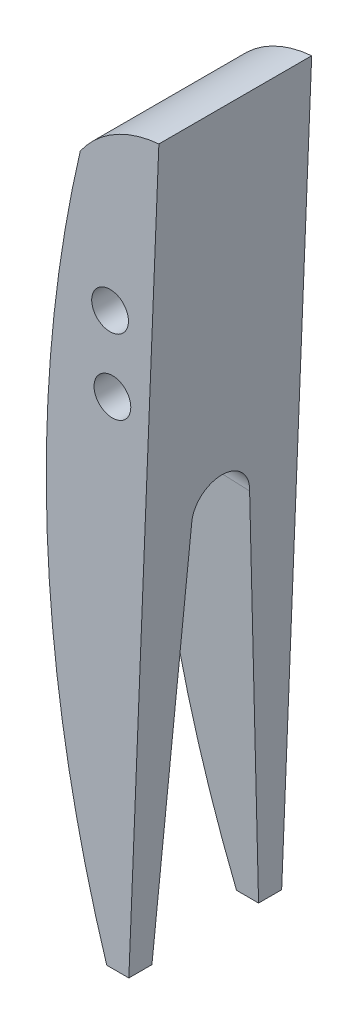
SolidWorks part; units mm, degrees
material "Polyester Resin"
ref_plane "Front Plane" through (0, 0, 0) normal (0, 0, 1) x (1, 0, 0)
ref_plane "Top Plane" through (0, 0, 0) normal (0, 1, 0) x (1, 0, 0)
ref_plane "Right Plane" through (0, 0, 0) normal (1, 0, 0) x (0, 0, -1)
sketch "Sketch1" plane through (0, 0, 0) normal (0, 0, 1) x (1, 0, 0)
  line L0 (23.5472, 52.9813) -> (117.7362, 52.9813) construction
  line L1 (74.1278, 88.7959) -> (72.0004, 36.5744)
  line L2 (672, 1512) -> (3360, 1512) construction
  arc A1 (68.9663, 85.8139) -> (72.0004, 36.5744) centre (153.2214, 66.2924) ccw
  circle A2 centre (70.9254, 77.7224) radius 1.2065
  circle A3 centre (71.0778, 72.8964) radius 1.2065
  arc A5 (74.1278, 88.7959) -> (68.9663, 85.8139) centre (74.7354, 81.7864) ccw
  dimension "D3" = 4.064
  dimension "D4" = 86.487
  dimension "D5" = 2.413
  dimension "D1" = 7.0358
  dimension "D7" = 11.43
  dimension "D2" = 3.81
  dimension "D6" = 82.296
  dimension "D8" = 4.826
  dimension "D9" = 0.1524
  dimension "D10" = 11.0735
  dimension "D11" = 41.148
extrude "Boss-Extrude1" add sketch "Sketch1" along normal blind 10.033
sketch "Sketch2" plane through (70.3936, -2.8677, 0) normal (0.9992, -0.0407, 0) x (0, 0, -1)
  line L1 (-10.033, 39.4748) -> (0, 39.4748) construction
  line L3 (-1.27, 39.4748) -> (-8.763, 39.4748)
  line L4 (-10.033, 39.4748) -> (-10.033, 91.7397) construction
  line L5 (0, 39.4748) -> (0, 91.7397) construction
  line L6 (-8.763, 39.4748) -> (-6.9215, 68.0498)
  line L7 (-1.27, 39.4748) -> (-3.1115, 68.0498)
  arc A0 (-3.1115, 68.0498) -> (-6.9215, 68.0498) centre (-5.0165, 68.0498) ccw
  dimension "D4" = 3.81
  dimension "D1" = 1.27
  dimension "D2" = 1.27
  dimension "D3" = 28.575
extrude "Cut-Extrude1" cut sketch "Sketch2" against normal blind 10.033
sketch "Sketch3" plane through (0, 0, 10.033) normal (0, 0, 1) x (1, 0, 0)
  line L0 (70.7044, 40.3898) -> (72.1559, 40.3898)
  line L1 (72.0004, 36.5744) -> (74.1278, 88.7959) construction
  line L2 (83.274, 40.3898) -> (71.717, 40.3898) construction
  line L3 (72.1559, 40.3898) -> (72.0004, 36.5744)
  arc A0 (68.9663, 85.8139) -> (72.0004, 36.5744) centre (153.2214, 66.2924) ccw construction
  arc A1 (70.7044, 40.3898) -> (72.0004, 36.5744) centre (153.2214, 66.2924) ccw
  arc A2 (66.7391, 65.3875) -> (72.0004, 36.5744) centre (153.2214, 66.2924) ccw construction
extrude "Cut-Extrude2" cut sketch "Sketch3" against normal up to surface (10.033 mm away) up to face at (70.3926, 70.5123, 0)
